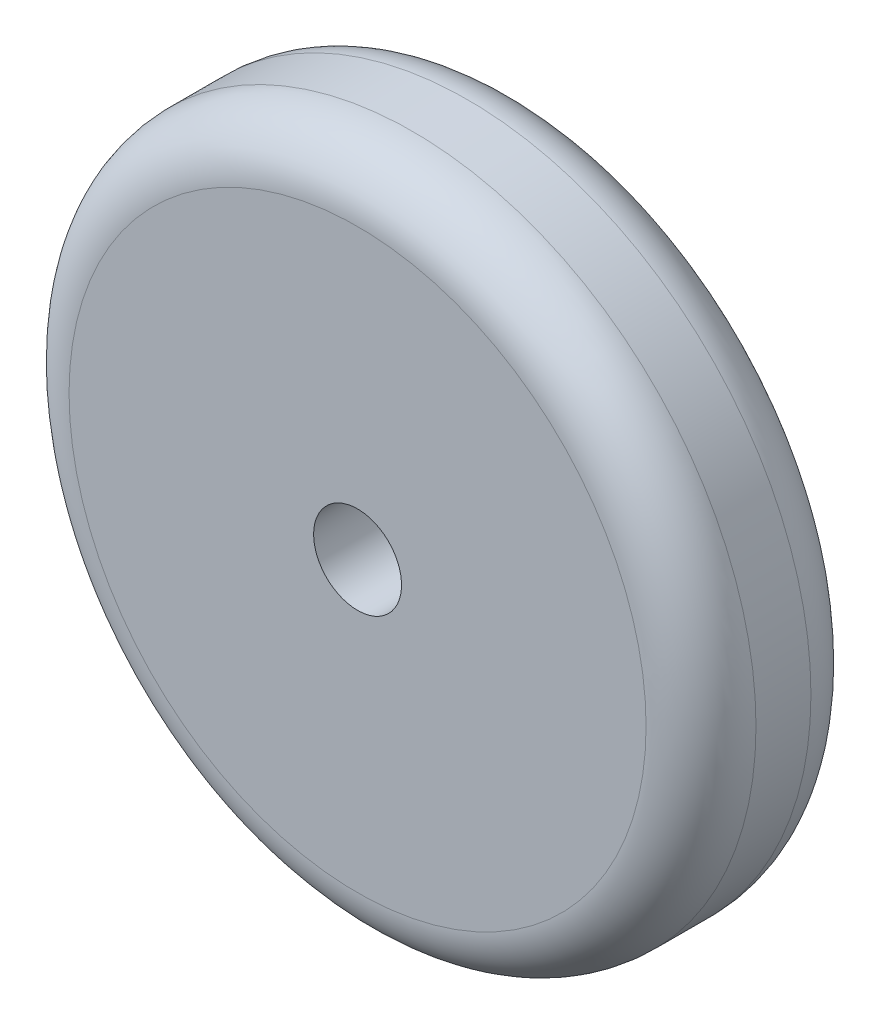
SolidWorks part; units mm, degrees
ref_plane "前视基准面" through (0, 0, 0) normal (0, 0, 1) x (1, 0, 0)
ref_plane "上视基准面" through (0, 0, 0) normal (0, 1, 0) x (1, 0, 0)
ref_plane "右视基准面" through (0, 0, 0) normal (1, 0, 0) x (0, 0, -1)
sketch "草图2" plane through (0, 0, 0) normal (0, 0, 1) x (1, 0, 0)
  circle A0 centre (0, 0) radius 62.5
  dimension "D1" = 125
extrude "凸台-拉伸1" add sketch "草图2" along normal blind 30
fillet "圆角1" radius 10 2 edges at (62.5, 0, 0) (62.5, 0, 30)
sketch "草图3" plane through (0, 0, 0) normal (0, 0, -1) x (-1, 0, 0)
  circle A0 centre (0, 0) radius 8
  dimension "D1" = 16
extrude "切除-拉伸1" cut sketch "草图3" against normal through all
